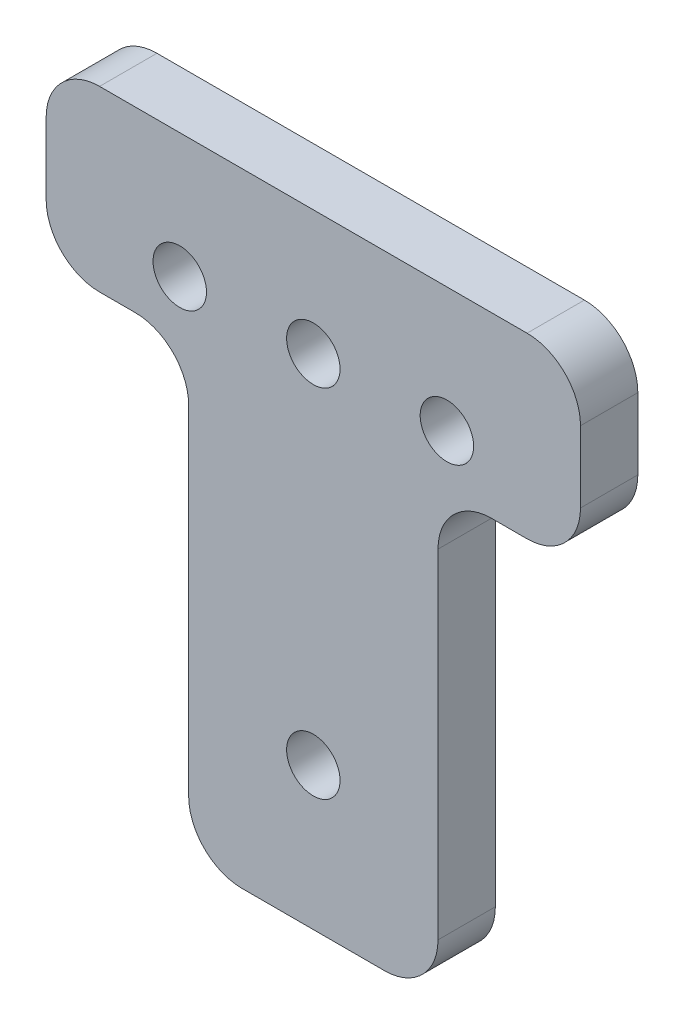
SolidWorks part; units mm, degrees
ref_plane "Front Plane" through (0, 0, 0) normal (0, 0, 1) x (1, 0, 0)
ref_plane "Top Plane" through (0, 0, 0) normal (0, 1, 0) x (1, 0, 0)
ref_plane "Right Plane" through (0, 0, 0) normal (1, 0, 0) x (0, 0, -1)
sketch "Sketch1" plane through (0, 0, 0) normal (0, 0, 1) x (1, 0, 0)
  line L0 (-7, 12.5) -> (-15, 12.5)
  line L1 (-7, -12.5) -> (7, -12.5)
  line L2 (-7, -12.5) -> (-7, 12.5)
  line L4 (7, -12.5) -> (7, 12.5)
  line L5 (-7, -12.5) -> (7, 12.5) construction
  line L6 (-7, 12.5) -> (7, -12.5) construction
  line L11 (-15, 12.5) -> (-15, 22.5)
  line L12 (-15, 22.5) -> (15, 22.5)
  line L13 (15, 22.5) -> (15, 12.5)
  line L14 (15, 12.5) -> (7, 12.5)
  line L15 (-15, 15.5) -> (-7.5, 15.5) construction
  line L16 (-7.5, 15.5) -> (0, 15.5) construction
  line L17 (0, 15.5) -> (7.5, 15.5) construction
  line L18 (7.5, 15.5) -> (15, 15.5) construction
  circle A0 centre (-7.5, 15.5) radius 1.5
  circle A1 centre (0, 15.5) radius 1.5
  circle A2 centre (7.5, 15.5) radius 1.5
  circle A3 centre (0, -4.5) radius 1.5
  point P0 (0, 0)
  point P20 (0, 0)
  dimension "D6" = 3
  dimension "D7" = 8
  dimension "D1" = 14
  dimension "D2" = 25
  dimension "D3" = 10
  dimension "D4" = 30
  dimension "D5" = 3
extrude "Boss-Extrude1" add sketch "Sketch1" along normal mid plane 3.22
fillet "Fillet1" radius 3 8 edges at (15, 22.5, 0) (15, 12.5, 0) (7, 12.5, 0) (7, -12.5, 0) (-7, -12.5, 0) (-7, 12.5, 0) (-15, 12.5, 0) (-15, 22.5, 0)
